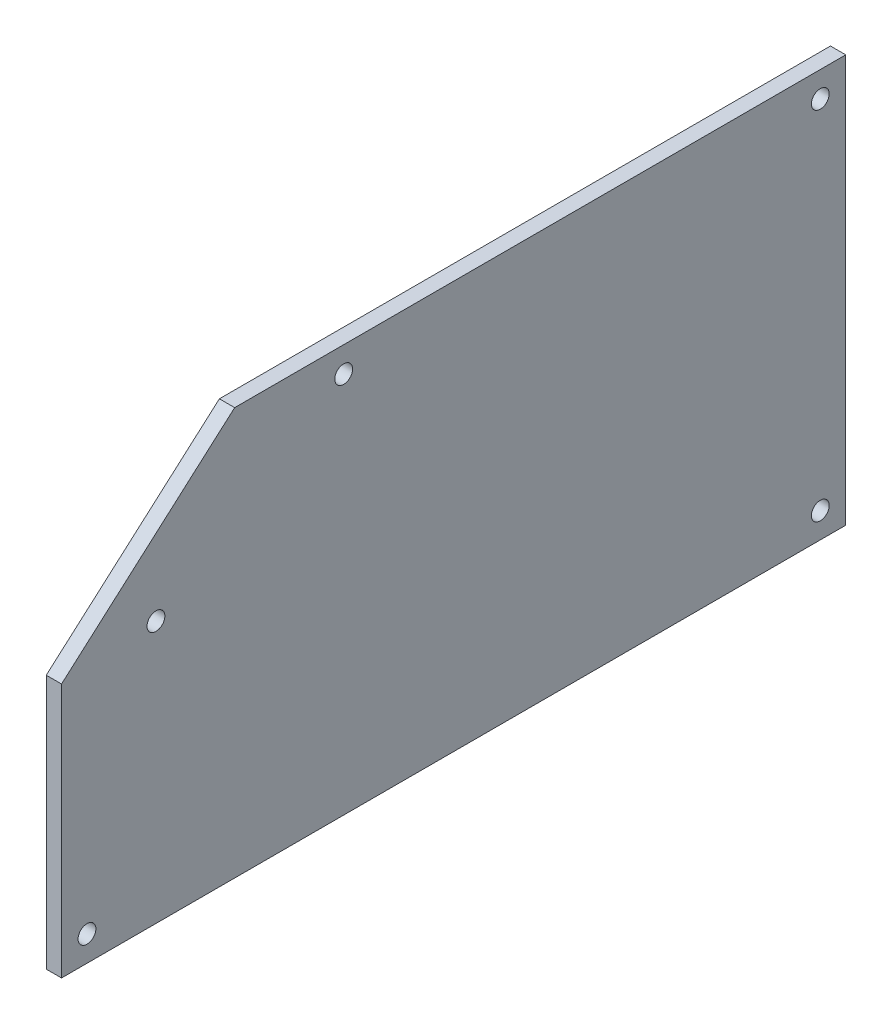
SolidWorks part; units mm, degrees
material "Acrylic (Medium-high impact)"
ref_plane "Front Plane" through (0, 0, 0) normal (0, 0, 1) x (1, 0, 0)
ref_plane "Top Plane" through (0, 0, 0) normal (0, 1, 0) x (1, 0, 0)
ref_plane "Right Plane" through (0, 0, 0) normal (1, 0, 0) x (0, 0, -1)
sketch "Sketch1" plane through (0, 0, 0) normal (1, 0, 0) x (0, 0, -1)
  line L0 (0, 0) -> (0, 50)
  line L1 (0, 50) -> (34, 80)
  line L2 (34, 80) -> (154, 80)
  line L3 (154, 80) -> (154, 0)
  line L4 (154, 0) -> (0, 0)
  dimension "D1" = 154
  dimension "D2" = 80
  dimension "D3" = 50
  dimension "D4" = 120
extrude "Boss-Extrude1" add sketch "Sketch1" along normal blind 3
sketch "Sketch2" plane through (0, 0, 0) normal (-1, 0, 0) x (0, 0, 1)
  line L0 (-149, 5) -> (-5, 5) construction
  line L1 (-5, 5) -> (-5, 47.7437) construction
  line L2 (-5, 47.7437) -> (-35.8905, 75) construction
  line L3 (-35.8905, 75) -> (-149, 75) construction
  line L4 (-149, 75) -> (-149, 5) construction
  line L5 (-154, 0) -> (0, 0)
  line L6 (0, 0) -> (0, 50)
  line L7 (0, 50) -> (-34, 80)
  line L8 (-34, 80) -> (-154, 80)
  line L9 (-154, 80) -> (-154, 0)
  line L10 (-154, 0) -> (0, 0) construction
  line L11 (0, 0) -> (0, 50) construction
  line L12 (0, 50) -> (-34, 80) construction
  line L13 (-34, 80) -> (-154, 80) construction
  line L14 (-154, 80) -> (-154, 0) construction
  line L15 (-47.9072, 72) -> (-62.9072, 72) construction
  line L16 (-47.9072, 72) -> (-62.9072, 72) construction
  line L17 (-44.8824, 80) -> (0, 40.3979) construction
  line L18 (-12.0915, 40.3979) -> (-47.9072, 72) construction
  line L19 (-44.8824, 80) -> (0, 40.3979) construction
  line L20 (-12.0915, 40.3979) -> (-47.9072, 72) construction
  line L21 (-42.074, 72.1876) -> (-11.189, 44.936) construction
  circle A0 centre (-149, 5) radius 1.75
  circle A1 centre (-149, 75) radius 1.75
  circle A2 centre (-5, 5) radius 1.75
  circle A3 centre (-55.4072, 75) radius 1.75
  circle A5 centre (-18.5408, 51.423) radius 1.75
  point P17 (-55.4072, 75)
  point P22 (-55.4072, 72)
  dimension "D3" = 3.5
  dimension "D4" = 3.5
  dimension "D5" = 3.5
  dimension "D6" = 3.5
  dimension "D7" = 4
  dimension "D8" = 3.5
  dimension "D9" = 23.577
  dimension "D1" = 0
  dimension "D2" = 5
extrude "Cut-Extrude1" cut sketch "Sketch2" against normal through all
